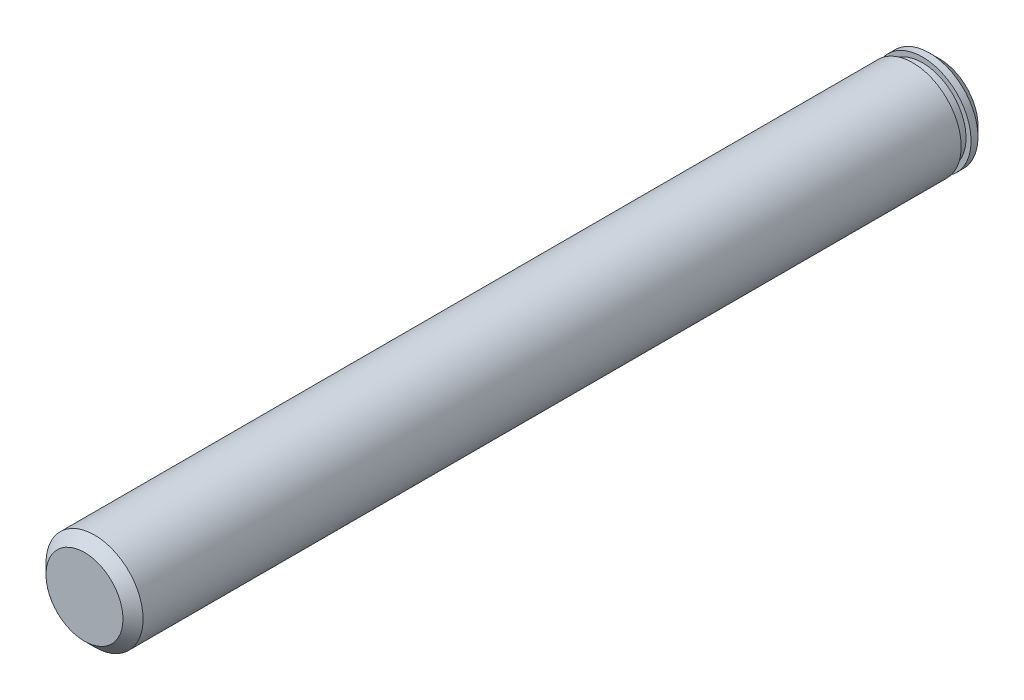
SolidWorks part; units mm, degrees
ref_plane "Front Plane" through (0, 0, 0) normal (0, 0, 1) x (1, 0, 0)
ref_plane "Top Plane" through (0, 0, 0) normal (0, 1, 0) x (1, 0, 0)
ref_plane "Right Plane" through (0, 0, 0) normal (1, 0, 0) x (0, 0, -1)
sketch "Sketch1" plane through (0, 0, 0) normal (0, 0, 1) x (1, 0, 0)
  circle A0 centre (0, 0) radius 4.825
  dimension "D1" = 9.65
extrude "Boss-Extrude1" add sketch "Sketch1" along normal blind 85
chamfer "Chamfer2" distance 1 angle 45 2 edges at (4.825, 0, 85) (4.825, 0, 0)
sketch "Sketch3" plane through (0, 0, 0) normal (0, 1, 0) x (1, 0, 0)
  line L0 (-4.825, -1) -> (-4.825, -84) construction
  line L1 (-4.825, -1.69) -> (-4.325, -1.69)
  line L2 (-4.825, -1.69) -> (-4.825, -2.67)
  line L3 (-4.825, -2.67) -> (-4.325, -2.67)
  line L4 (-4.325, -1.69) -> (-4.325, -2.67)
  line L5 (0, 0) -> (0, -3.7256) construction
  dimension "D1" = 0.98
  dimension "D2" = 0.5
  dimension "D3" = 0.69
revolve "Cut-Revolve4" cut sketch "Sketch3" angle 360 about L5
